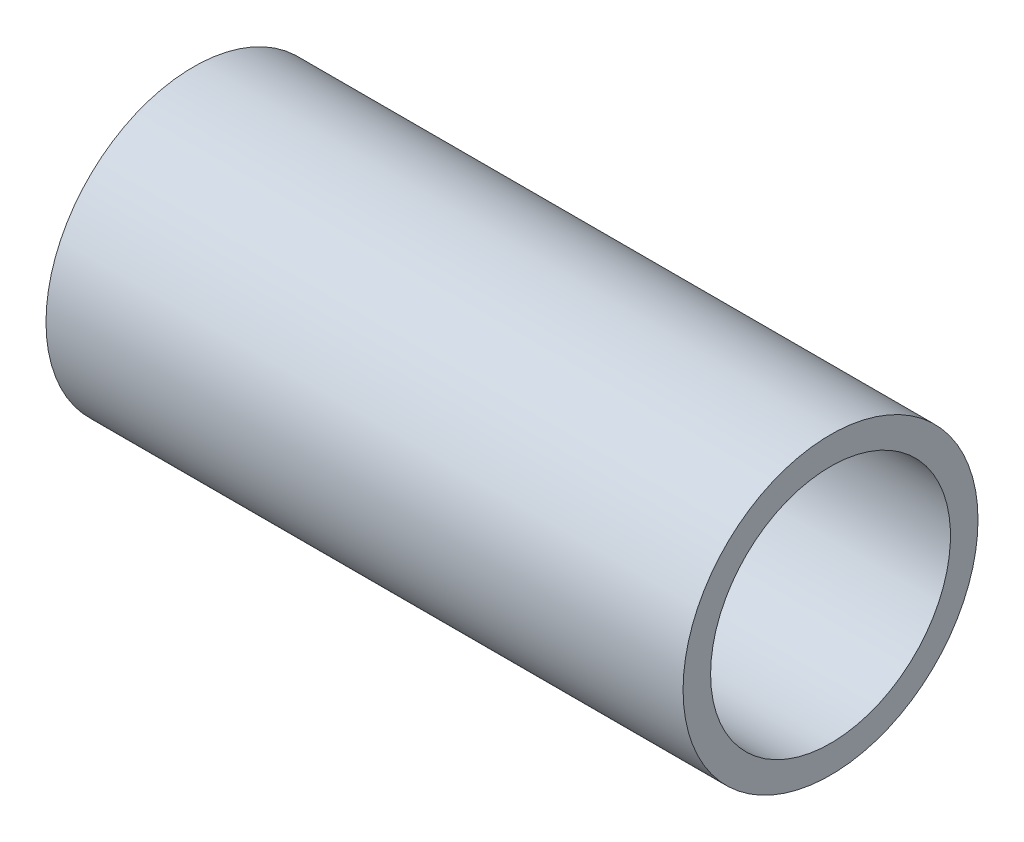
SolidWorks part; units mm, degrees
ref_plane "Plane1" through (0, 0, 0) normal (0, 0, 1) x (1, 0, 0)
ref_plane "Plane2" through (0, 0, 0) normal (0, 1, 0) x (1, 0, 0)
ref_plane "Plane3" through (0, 0, 0) normal (1, 0, 0) x (0, 0, -1)
sketch "Sketch1" plane through (0, 0, 0) normal (0, 0, 1) x (1, 0, 0)
  line L0 (0, 0) -> (70.6566, 0) construction
  line L1 (0, 0) -> (0, 37.5) construction
  line L2 (-81, 37.5) -> (81, 37.5)
  line L3 (81, 37.5) -> (81, 30.5)
  line L4 (81, 30.5) -> (-81, 30.5)
  line L5 (-81, 37.5) -> (-81, 30.5)
  point P8 (0, 30.5)
  dimension "D1" = 75
  dimension "D2" = 61
  dimension "D3" = 162
revolve "Revolve1" add sketch "Sketch1" angle 360 about L0
